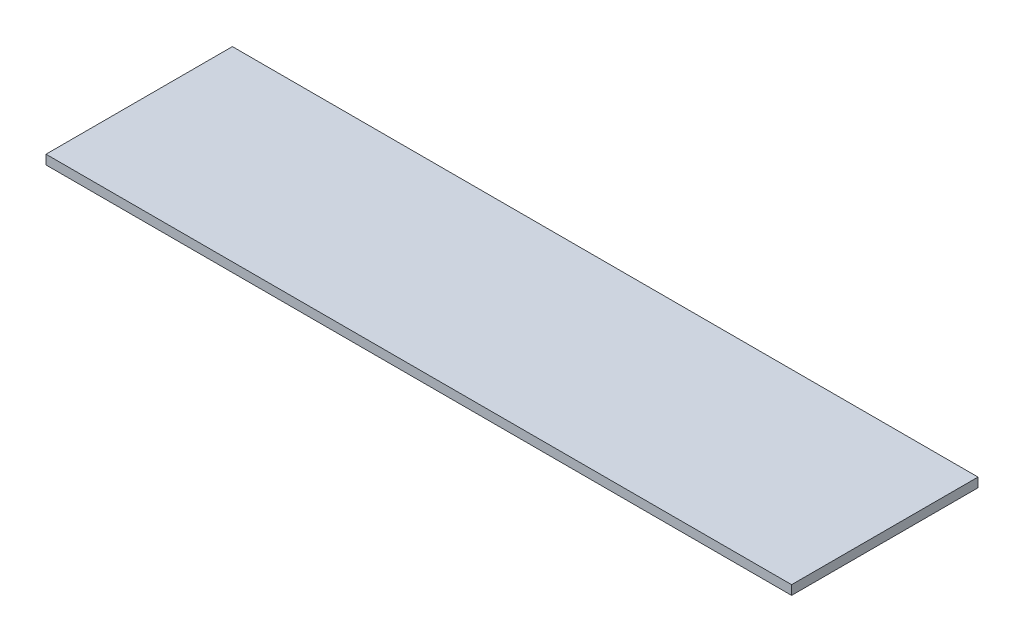
SolidWorks part; units mm, degrees
ref_plane "Front Plane" through (0, 0, 0) normal (0, 0, 1) x (1, 0, 0)
ref_plane "Top Plane" through (0, 0, 0) normal (0, 1, 0) x (1, 0, 0)
ref_plane "Right Plane" through (0, 0, 0) normal (1, 0, 0) x (0, 0, -1)
sketch "Sketch1" plane through (0, 0, 0) normal (0, 1, 0) x (1, 0, 0)
  line L1 (-40, -10) -> (40, -10)
  line L2 (-40, -10) -> (-40, 10)
  line L3 (-40, 10) -> (40, 10)
  line L4 (40, -10) -> (40, 10)
  line L5 (-40, -10) -> (40, 10) construction
  line L6 (-40, 10) -> (40, -10) construction
  point P0 (0, 0)
  dimension "D1" = 80
  dimension "D2" = 20
extrude "Boss-Extrude1" add sketch "Sketch1" along normal blind 1 contours L3 L4 L1 L2
